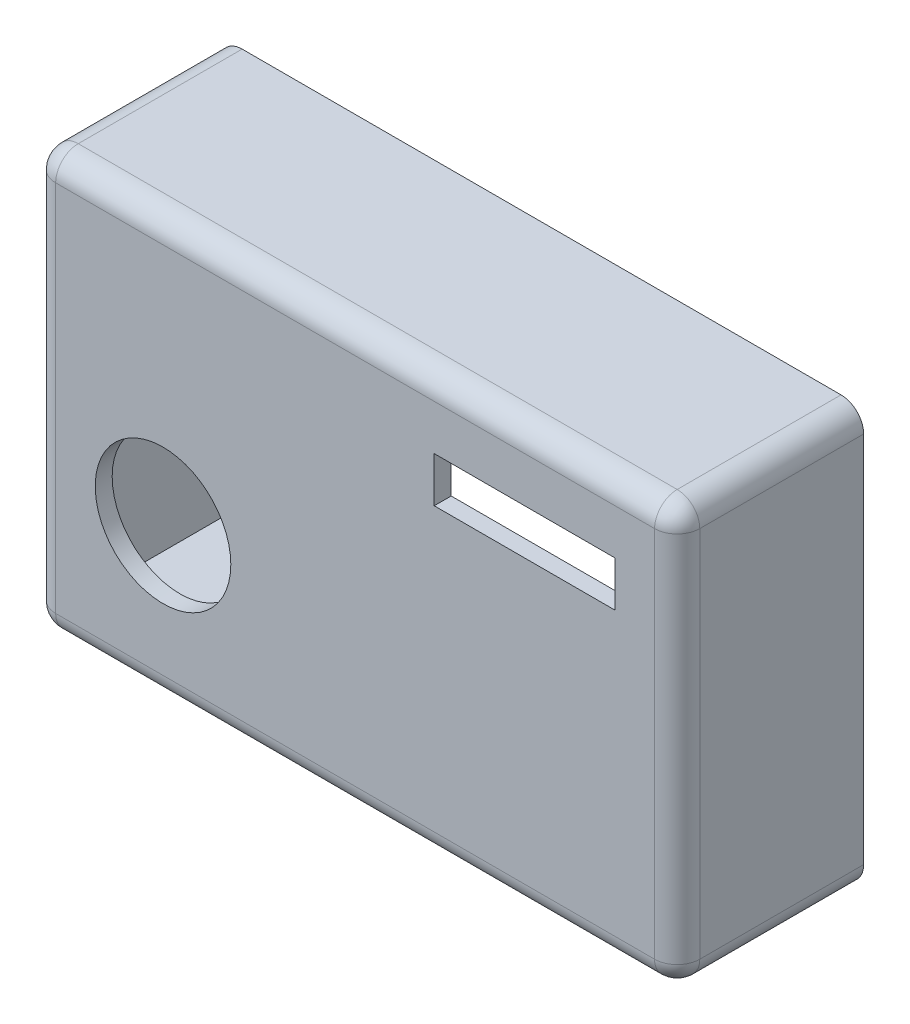
SolidWorks part; units mm, degrees
ref_plane "Front Plane" through (0, 0, 0) normal (0, 0, 1) x (1, 0, 0)
ref_plane "Top Plane" through (0, 0, 0) normal (0, 1, 0) x (1, 0, 0)
ref_plane "Right Plane" through (0, 0, 0) normal (1, 0, 0) x (0, 0, -1)
sketch "Sketch1" plane through (0, 0, 0) normal (0, 0, 1) x (1, 0, 0)
  line L0 (0, 0) -> (0, -17) construction
  line L5 (-27, -17) -> (-7.5, -17)
  line L6 (-27, -17) -> (-27, 17)
  line L7 (-27, 17) -> (27, 17)
  line L8 (27, -17) -> (27, 17)
  line L9 (-27, -17) -> (27, 17) construction
  line L10 (-27, 17) -> (27, -17) construction
  line L11 (7.5, -17) -> (27, -17)
  line L16 (-7.5, -17) -> (7.5, -17)
  point P0 (0, 0)
  dimension "D1" = 54
  dimension "D2" = 34
extrude "Boss-Extrude1" add sketch "Sketch1" along normal blind 1.5
sketch "Sketch2" plane through (0, 0, 1.5) normal (0, 0, 1) x (1, 0, 0)
  line L0 (-1000, 0) -> (49000, 0) construction
  line L1 (0, -1000) -> (0, 49000) construction
  line L2 (23, 12.5) -> (7, 12.5)
  line L7 (23, 12.5) -> (23, 8.5)
  line L8 (7, 12.5) -> (7, 8.5)
  line L9 (23, 8.5) -> (7, 8.5)
  line L10 (27, 17) -> (-27, 17) construction
  line L11 (27, -17) -> (27, 17) construction
  line L12 (-27, 17) -> (-27, -17) construction
  line L13 (-27, -17) -> (27, -17) construction
  circle A0 centre (-17, -5) radius 6
  dimension "D5" = 12
  dimension "D1" = 16
  dimension "D2" = 4
  dimension "D3" = 8.5
  dimension "D4" = 4
  dimension "D6" = 10
  dimension "D7" = 12
extrude "Cut-Extrude1" cut sketch "Sketch2" against normal blind 2
sketch "Sketch3" plane through (0, 0, 0) normal (0, 0, -1) x (-1, 0, 0)
  line L0 (-27, 17) -> (-27, -17)
  line L1 (-27, -17) -> (27, -17)
  line L2 (27, 17) -> (27, -17) construction
  line L3 (27, -17) -> (-27, -17) construction
  line L4 (27, -17) -> (27, 17)
  line L5 (27, 17) -> (-27, 17)
  line L10 (-28.5, 18.5) -> (28.5, 18.5)
  line L11 (-28.5, 18.5) -> (-28.5, -18.5)
  line L12 (28.5, 18.5) -> (28.5, -18.5)
  line L13 (-28.5, -18.5) -> (28.5, -18.5)
  dimension "D1" = 1.5
  dimension "D2" = 1.5
  dimension "D3" = 1.5
  dimension "D4" = 1.5
extrude "Boss-Extrude2" add sketch "Sketch3" along normal blind 15 and the other way blind 1.5
fillet "Fillet1" radius 2 8 edges at (-28.5, 0, 1.5) (0, -18.5, 1.5) (0, 18.5, 1.5) (28.5, 0, 1.5) (28.5, 18.5, -6.75) (28.5, -18.5, -6.75) (-28.5, -18.5, -6.75) (-28.5, 18.5, -6.75)
